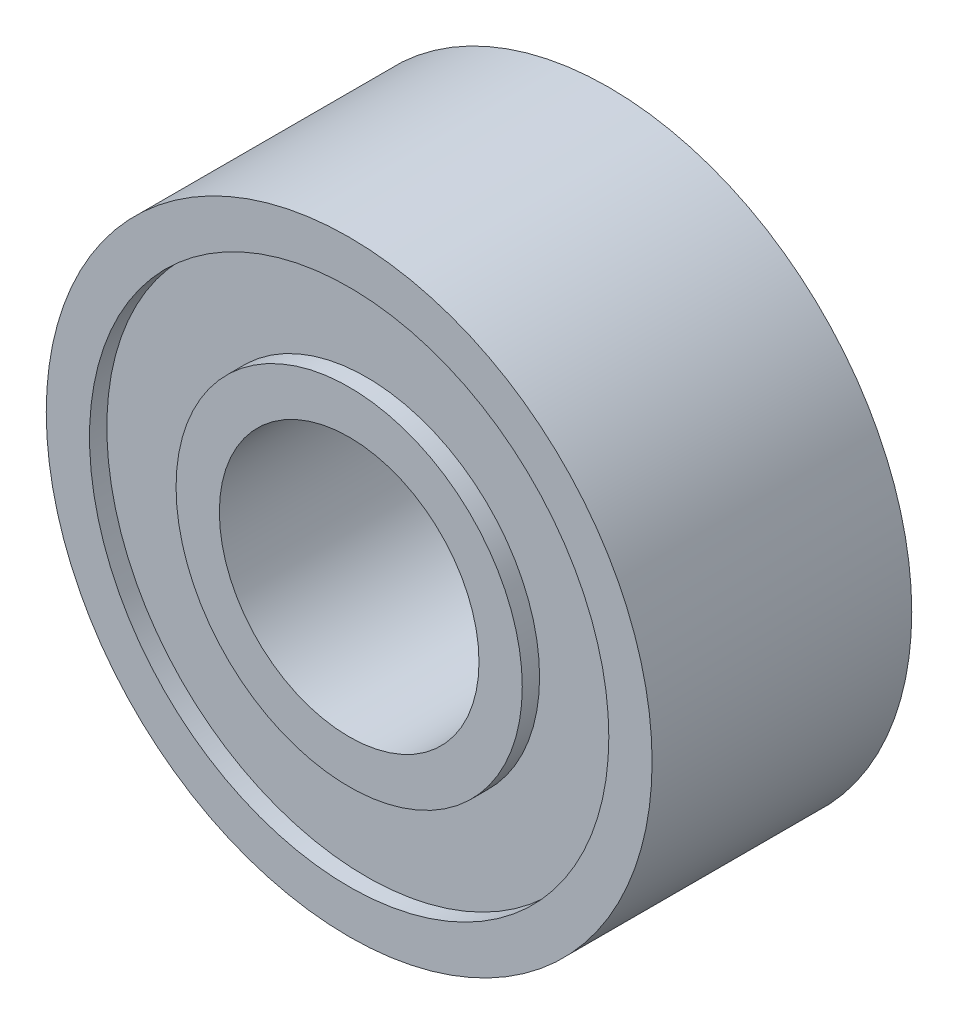
SolidWorks part; units mm, degrees
ref_plane "Front Plane" through (0, 0, 0) normal (0, 0, 1) x (1, 0, 0)
ref_plane "Top Plane" through (0, 0, 0) normal (0, 1, 0) x (1, 0, 0)
ref_plane "Right Plane" through (0, 0, 0) normal (1, 0, 0) x (0, 0, -1)
sketch "Sketch1" plane through (0, 0, 0) normal (0, 0, 1) x (1, 0, 0)
  circle A0 centre (0, 0) radius 3.5
  circle A1 centre (0, 0) radius 1.5
  dimension "D1" = 3
  dimension "D2" = 7
extrude "Boss-Extrude1" add sketch "Sketch1" along normal blind 3
sketch "Sketch2" plane through (0, 0, 3) normal (0, 0, 1) x (1, 0, 0)
  circle A3 centre (0, 0) radius 3
  circle A4 centre (0, 0) radius 3.5 construction
  circle A5 centre (0, 0) radius 2
  circle A6 centre (0, 0) radius 1.5 construction
  dimension "D1" = 0.5
  dimension "D2" = 0.5
extrude "Cut-Extrude1" cut sketch "Sketch2" against normal blind 3
sketch "Sketch3" plane through (0, 0, 3) normal (0, 0, 1) x (1, 0, 0)
  circle A0 centre (0, 0) radius 2
  circle A1 centre (0, 0) radius 3
extrude "Boss-Extrude3" add sketch "Sketch3" against normal blind 2.8 separate body
sketch "Sketch4" plane through (0, 0, 3) normal (0, 0, 1) x (1, 0, 0)
  circle A0 centre (0, 0) radius 2
  circle A1 centre (0, 0) radius 3
extrude "Cut-Extrude2" cut sketch "Sketch4" against normal blind 0.2
